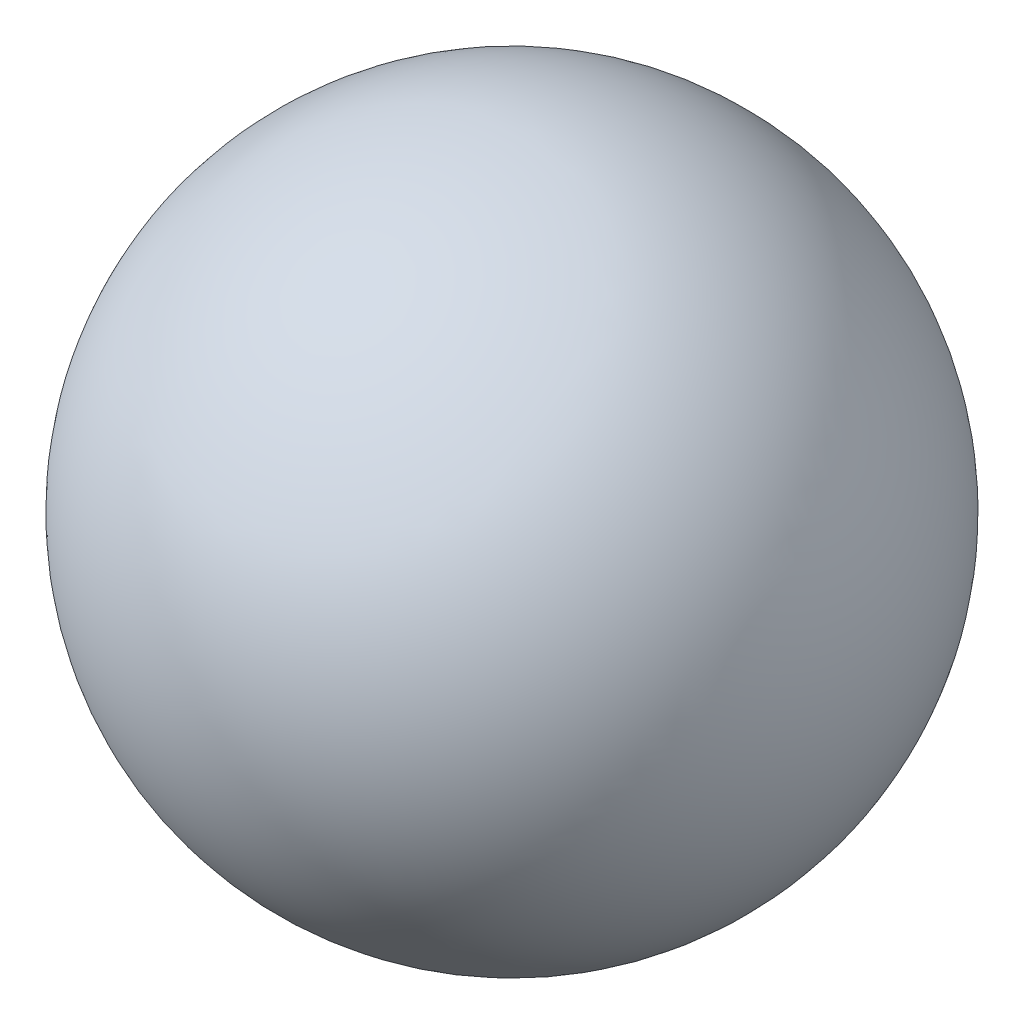
SolidWorks part; units mm, degrees
ref_plane "Front Plane" through (0, 0, 0) normal (0, 0, 1) x (1, 0, 0)
ref_plane "Top Plane" through (0, 0, 0) normal (0, 1, 0) x (1, 0, 0)
ref_plane "Right Plane" through (0, 0, 0) normal (1, 0, 0) x (0, 0, -1)
other "Configuration Table"
sketch "草图1" plane through (0, 0, 0) normal (0, 0, 1) x (1, 0, 0)
  line L0 (0, 0) -> (0, 6.6294) construction
  line L1 (-5, 0) -> (-3, 0)
  line L2 (3, 0) -> (5, 0)
  arc A0 (3, 0) -> (-3, 0) centre (0, 0) ccw
  arc A1 (5, 0) -> (-5, 0) centre (0, 0) ccw
  circle A2 centre (0, 0) radius 5 construction
  circle A3 centre (0, 0) radius 3 construction
  dimension "D1" = 2
revolve "旋转3" add sketch "草图1" angle 360 about L1
